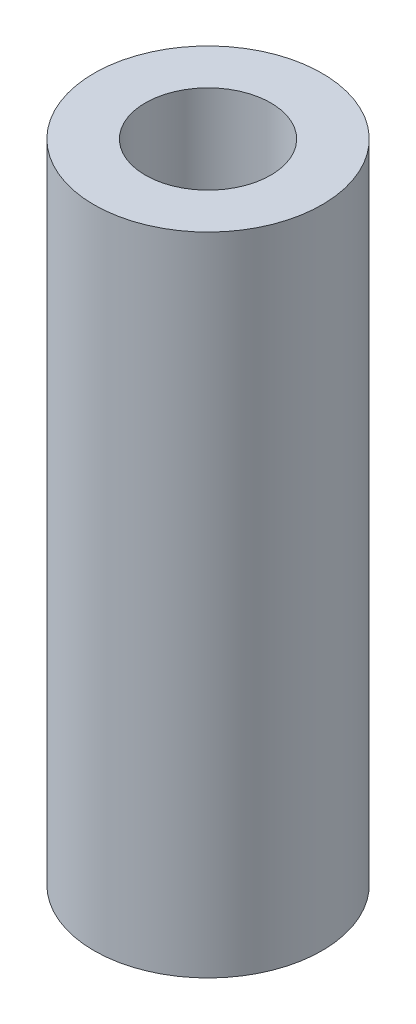
SolidWorks part; units mm, degrees
ref_plane "Front Plane" through (0, 0, 0) normal (0, 0, 1) x (1, 0, 0)
ref_plane "Top Plane" through (0, 0, 0) normal (0, 1, 0) x (1, 0, 0)
ref_plane "Right Plane" through (0, 0, 0) normal (1, 0, 0) x (0, 0, -1)
sketch "Sketch2" plane through (0, 143.5657, 0) normal (0, 1, 0) x (1, 0, 0)
  circle A0 centre (5.0369, -260.7579) radius 1.65 construction
  circle A1 centre (5.0369, -260.7579) radius 3 construction
  circle A2 centre (5.0369, -260.7579) radius 1.65
  circle A3 centre (5.0369, -260.7579) radius 3
extrude "Boss-Extrude1" add sketch "Sketch2" along normal blind 17
